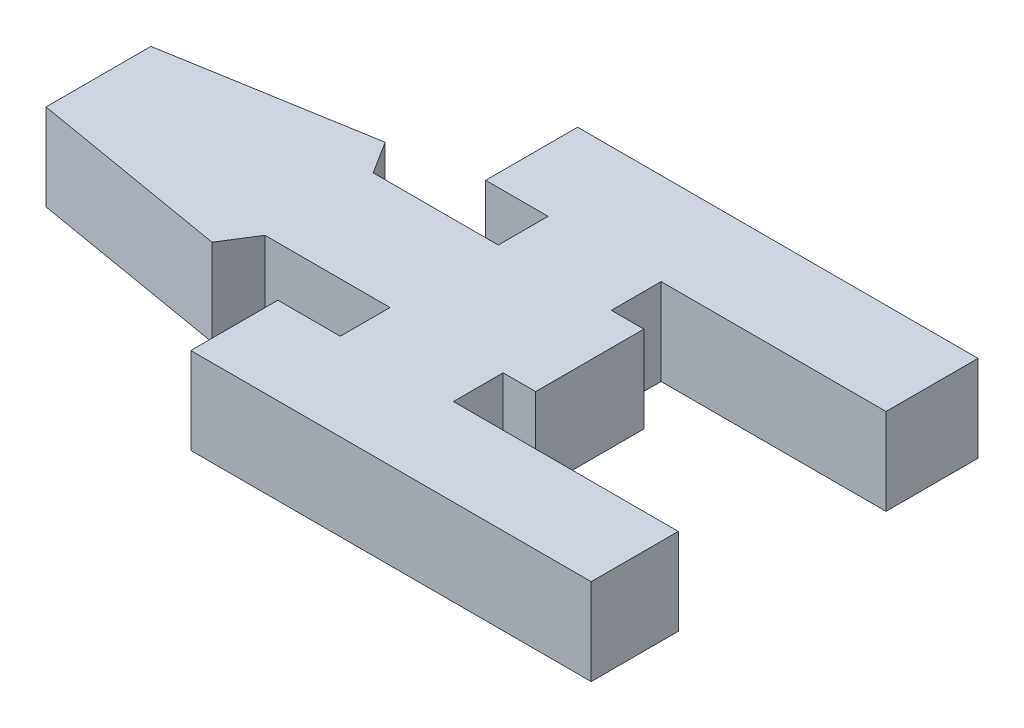
SolidWorks part; units mm, degrees
ref_plane "Front Plane" through (0, 0, 0) normal (0, 0, 1) x (1, 0, 0)
ref_plane "Top Plane" through (0, 0, 0) normal (0, 1, 0) x (1, 0, 0)
ref_plane "Right Plane" through (0, 0, 0) normal (1, 0, 0) x (0, 0, -1)
sketch "Sketch1" plane through (0, 0, 0) normal (0, 1, 0) x (1, 0, 0)
  line L0 (185.4606, 495.8819) -> (928.1273, 495.8819) construction
  line L1 (35.7855, 49.6193) -> (37.6764, 46.6193)
  line L2 (17.2873, 46.467) -> (35.7855, 49.6193)
  line L3 (43.4731, 59.7193) -> (80.4731, 59.7193)
  line L4 (43.4731, 59.7193) -> (43.4731, 51.2193)
  line L5 (43.4731, 51.2193) -> (49.2388, 51.2193)
  line L6 (80.4731, 59.7193) -> (80.4731, 51.2193)
  line L7 (80.4731, 32.0193) -> (59.6891, 32.0193)
  line L8 (80.4731, 32.0193) -> (80.4731, 23.9714)
  line L9 (80.4731, 23.9714) -> (43.4731, 23.9714)
  line L10 (43.4731, 32.0193) -> (43.4731, 23.9714)
  line L11 (37.6764, 46.6193) -> (49.2388, 46.6193)
  line L12 (49.2388, 36.6193) -> (49.2388, 32.0193)
  line L13 (37.6764, 36.6193) -> (49.2388, 36.6193)
  line L14 (62.6921, 46.6193) -> (62.6921, 36.6193)
  line L15 (49.2388, 32.0193) -> (43.4731, 32.0193)
  line L16 (49.2388, 51.2193) -> (49.2388, 46.6193)
  line L18 (59.6891, 51.2193) -> (59.6891, 46.6193)
  line L19 (59.6891, 36.6193) -> (62.6921, 36.6193)
  line L21 (59.6891, 36.6193) -> (59.6891, 32.0193)
  line L22 (17.2873, 46.467) -> (17.2873, 36.7743)
  line L23 (35.7855, 33.6193) -> (17.2873, 36.7743)
  line L25 (59.6891, 46.6193) -> (62.6921, 46.6193)
  line L26 (59.6891, 51.2193) -> (80.4731, 51.2193)
  line L27 (37.6764, 36.6193) -> (35.7855, 33.6193)
  dimension "D3" = 3.1523
  dimension "D6" = 3.003
  dimension "D7" = 10
  dimension "D8" = 3.003
  dimension "D9" = 4.6
  dimension "D10" = 4.6
  dimension "D11" = 8.0479
  dimension "D12" = 8.5
  dimension "D13" = 37
  dimension "D14" = 37
  dimension "D15" = 3.155
  dimension "D16" = 18.4982
extrude "Boss-Extrude1" add sketch "Sketch1" along normal blind 8
sketch "Sketch2" plane through (0, 0, 0) normal (0, -1, 0) x (1, 0, 0)
  line L0 (17.2873, -41.6207) -> (62.6921, -41.6193) construction
  line L1 (17.2873, -46.467) -> (17.2873, -36.7743) construction
  line L2 (62.6921, -36.6193) -> (62.6921, -46.6193) construction
  line L3 (47.8852, -36.6193) -> (47.8852, -46.6193) construction
  line L4 (37.6764, -36.6193) -> (49.2388, -36.6193) construction
  line L5 (49.2388, -46.6193) -> (37.6764, -46.6193) construction
  circle A0 centre (49.0873, -41.6197) radius 2.5
  dimension "D1" = 31.8
  dimension "D2" = 45.4048
extrude "Boss-Extrude2" add sketch "Sketch2" along normal blind 6
